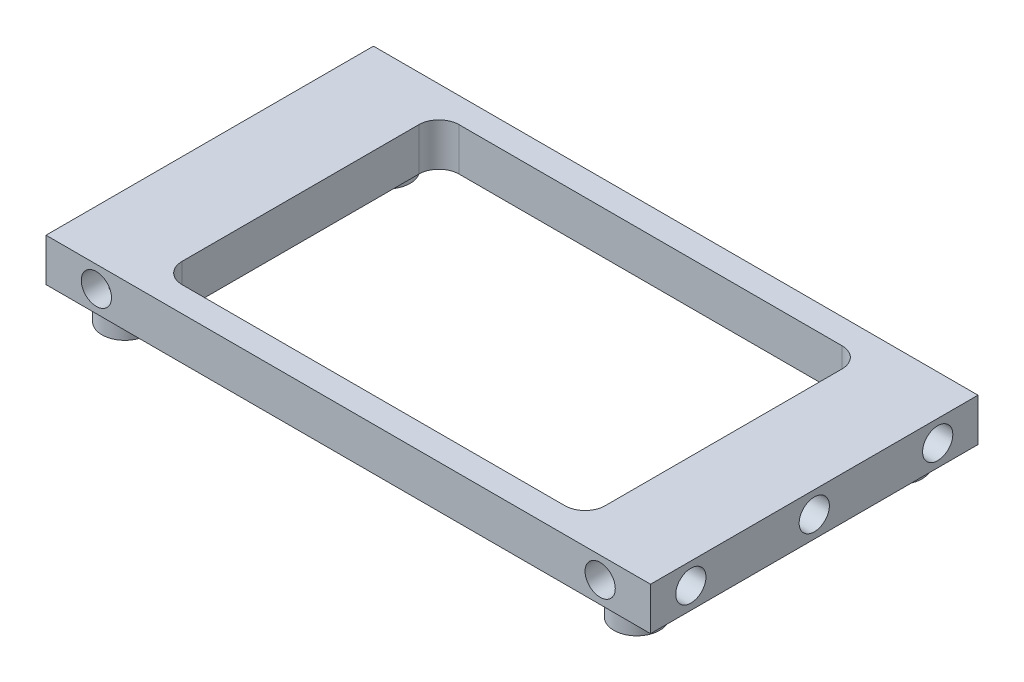
SolidWorks part; units mm, degrees
ref_plane "Front Plane" through (0, 0, 0) normal (0, 0, 1) x (1, 0, 0)
ref_plane "Top Plane" through (0, 0, 0) normal (0, 1, 0) x (1, 0, 0)
ref_plane "Right Plane" through (0, 0, 0) normal (1, 0, 0) x (0, 0, -1)
sketch "Sketch1" plane through (0, 0, 0) normal (1, 0, 0) x (0, 0, -1)
  line L1 (-32.5, -4.25) -> (32.5, -4.25)
  line L2 (-32.5, -4.25) -> (-32.5, 4.25)
  line L3 (-32.5, 4.25) -> (32.5, 4.25)
  line L4 (32.5, -4.25) -> (32.5, 4.25)
  line L5 (-32.5, -4.25) -> (32.5, 4.25) construction
  line L6 (-32.5, 4.25) -> (32.5, -4.25) construction
  point P0 (0, 0)
  dimension "D1" = 8.5
  dimension "D2" = 65
extrude "Boss-Extrude1" add sketch "Sketch1" along normal blind 120
hole_wizard "Ø6.0mm Dowel Hole1" positions "Sketch2" profile "Sketch3" hole size "Ø6.0" standard "ANSI Metric"
sketch "Sketch2" plane through (120, 0, 0) normal (1, 0, 0) x (0, 0, -1)
  line L0 (-32.5, 4.25) -> (-32.5, -4.25) construction
  line L1 (32.5, -4.25) -> (32.5, 4.25) construction
  point P0 (-24.5, 0)
  point P2 (0, 0)
  point P5 (24.5, 0)
  dimension "D1" = 8
  dimension "D2" = 8
sketch "Sketch3" plane through (120, 0, 24.5) normal (0, 1, 0) x (0, 0, -1)
  line L0 (0, 0) -> (0, 11.8026)
  line L1 (0, 11.8026) -> (3, 10)
  line L2 (3, 10) -> (3, 0)
  line L5 (3, 0) -> (0, 0)
  line L10 (0, 11.8026) -> (-3, 10) construction
  line L11 (0, -6.35) -> (0, 107.95) construction
  dimension "Hole Dia." = 6
  dimension "Hole Depth" = 10
  dimension "Drill Angle" = 118
ref_plane "Plane1" through (60, 0, 0) normal (1, 0, 0) x (0, 0, -1)
mirror "Mirror1" about plane through (60, 0, 0) normal (1, 0, 0) of "Ø6.0mm Dowel Hole1"
hole_wizard "Ø6.0mm Dowel Hole2" positions "Sketch4" profile "Sketch5" hole size "Ø6.0" standard "ANSI Metric"
sketch "Sketch4" plane through (0, 0, -32.5) normal (0, 0, -1) x (-1, 0, 0)
  line L0 (-120, -4.25) -> (-120, 4.25) construction
  line L1 (0, -4.25) -> (0, 4.25) construction
  line L2 (-120, 0) -> (0, 0) construction
  point P0 (-110, 0)
  point P2 (-10, 0)
  dimension "D1" = 10
  dimension "D2" = 10
sketch "Sketch5" plane through (110, 0, -32.5) normal (1, 0, 0) x (0, 1, 0)
  line L0 (0, 0) -> (0, 9.8026)
  line L1 (0, 9.8026) -> (3, 8)
  line L2 (3, 8) -> (3, 0)
  line L5 (3, 0) -> (0, 0)
  line L10 (0, 9.8026) -> (-3, 8) construction
  line L11 (0, -6.35) -> (0, 107.95) construction
  dimension "Hole Dia." = 6
  dimension "Hole Depth" = 8
  dimension "Drill Angle" = 118
mirror "Mirror2" about plane through (0, 0, 0) normal (0, 0, 1) of "Ø6.0mm Dowel Hole2"
sketch "Sketch6" plane through (0, 4.25, 0) normal (0, 1, 0) x (1, 0, 0)
  line L0 (86, -7) -> (86, 7) construction
  line L1 (80, -7) -> (80, 7)
  line L2 (92, -7) -> (92, 7)
  line L3 (120, 32.5) -> (120, -32.5) construction
  arc A0 (80, -7) -> (92, -7) centre (86, -7) ccw
  arc A1 (92, 7) -> (80, 7) centre (86, 7) ccw
  point P2 (86, 0)
  point P10 (120, 0)
  dimension "D3" = 12
  dimension "D1" = 40
  dimension "D2" = 14
extrude "Cut-Extrude1" cut sketch "Sketch6" against normal through all
mirror "Mirror3" about plane through (60, 0, 0) normal (1, 0, 0) of "Cut-Extrude1"
sketch "Sketch7" plane through (0, 4.25, 0) normal (0, 1, 0) x (1, 0, 0)
  line L0 (120, 32.5) -> (0, 32.5) construction
  line L1 (87, 17) -> (33, 17)
  line L2 (87, 17) -> (87, -17)
  line L3 (87, -17) -> (33, -17)
  line L4 (33, 17) -> (33, -17)
  line L5 (87, 17) -> (33, -17) construction
  line L6 (87, -17) -> (33, 17) construction
  point P0 (60, 0)
  point P8 (60, 32.5)
  dimension "D1" = 54
  dimension "D2" = 34
hole_wizard "Ø3.0mm Dowel Hole1" positions "Sketch8" profile "Sketch9" hole size "Ø3.0" standard "ANSI Metric" end condition through all
sketch "Sketch8" plane through (0, 4.25, 0) normal (0, 1, 0) x (1, 0, 0)
  line L0 (120, -32.5) -> (0, -32.5) construction
  line L1 (120, 32.5) -> (0, 32.5) construction
  line L2 (120, 32.5) -> (120, -32.5) construction
  line L3 (0, 32.5) -> (0, -32.5) construction
  point P0 (87, -17)
  point P3 (87, 17)
  point P6 (33, 17)
  point P9 (33, -17)
  point P13 (100, -24.5)
  point P15 (60, -24.5)
  point P17 (20, -24.5)
  point P19 (100, 24.5)
  point P21 (60, 24.5)
  point P23 (20, 24.5)
  point P40 (60, 32.5)
  dimension "D1" = 8
  dimension "D2" = 8
  dimension "D3" = 20
  dimension "D4" = 20
sketch "Sketch9" plane through (87, 4.25, 17) normal (1, 0, 0) x (0, 0, 1)
  line L0 (0, 0) -> (0, 8.5)
  line L1 (0, 8.5) -> (1.75, 8.5)
  line L2 (1.75, 8.5) -> (1.75, 0)
  line L5 (1.75, 0) -> (0, 0)
  line L11 (0, -6.35) -> (0, 107.95) construction
  dimension "Thru Hole Dia." = 3.5
  dimension "Thru Hole Depth" = 8.5
sketch "Sketch10" plane through (0, -4.25, 0) normal (0, -1, 0) x (1, 0, 0)
  line L0 (120, 32.5) -> (0, 32.5) construction
  line L1 (40, -21.5) -> (80, -21.5)
  line L2 (40, -21.5) -> (40, 21.5)
  line L3 (40, 21.5) -> (80, 21.5)
  line L4 (80, -21.5) -> (80, 21.5)
  line L5 (40, -21.5) -> (80, 21.5) construction
  line L6 (40, 21.5) -> (80, -21.5) construction
  line L7 (0, 32.5) -> (0, -32.5) construction
  line L8 (40, 21.5) -> (34, 13)
  line L9 (34, -13) -> (40, -21.5)
  line L10 (40, -7) -> (40, 7) construction
  line L11 (80, 21.5) -> (86, 13)
  line L12 (86, -13) -> (80, -21.5)
  arc A0 (40, 7) -> (28, 7) centre (34, 7) ccw construction
  arc A1 (28, -7) -> (40, -7) centre (34, -7) ccw construction
  arc A2 (28, -7) -> (40, -7) centre (34, -7) ccw
  arc A3 (40, 7) -> (28, 7) centre (34, 7) ccw
  arc A4 (80, -7) -> (92, -7) centre (86, -7) ccw construction
  arc A5 (92, 7) -> (80, 7) centre (86, 7) ccw construction
  arc A6 (80, -7) -> (92, -7) centre (86, -7) ccw
  arc A7 (92, 7) -> (80, 7) centre (86, 7) ccw
  point P0 (60, 0)
  point P7 (60, 32.5)
  point P11 (0, 0)
  line M17 (80, -7) -> (80, 7)
  arc M18 (80, 7) -> (92, 7) centre (86, 7) cw
  arc M20 (92, -7) -> (80, -7) centre (86, -7) cw
  arc M21 (28, 7) -> (40, 7) centre (34, 7) cw
  line M22 (40, 7) -> (40, -7)
  arc M23 (40, -7) -> (28, -7) centre (34, -7) cw
  dimension "D1" = 43
extrude "Cut-Extrude2" cut sketch "Sketch10" against normal through all contours L2 L8 M21 | L1 L4 L3 L2 M17 M22 | L9 L2 M23 | L11 L4 M18 | L12 L4 M20
fillet "Fillet1" radius 6 8 edges at (34, 0, -13) (40, 0, -21.5) (34, 0, 13) (40, 0, 21.5) (80, 0, -21.5) (86, 0, -13) (80, 0, 21.5) (86, 0, 13)
sketch "Sketch11" plane through (0, -4.25, 0) normal (0, -1, 0) x (1, 0, 0)
  line L0 (120, 32.5) -> (0, 32.5) construction
  line L1 (110.8, -26.035) -> (9.2, -26.035)
  line L2 (110.8, -26.035) -> (110.8, 26.035)
  line L3 (110.8, 26.035) -> (9.2, 26.035)
  line L4 (9.2, -26.035) -> (9.2, 26.035)
  line L5 (110.8, -26.035) -> (9.2, 26.035) construction
  line L6 (110.8, 26.035) -> (9.2, -26.035) construction
  line L7 (120, 32.5) -> (120, -32.5) construction
  circle A0 centre (9.2, 26.035) radius 2.55
  circle A1 centre (110.8, 26.035) radius 2.55
  circle A2 centre (110.8, -26.035) radius 2.55
  circle A3 centre (9.2, -26.035) radius 2.55
  circle A4 centre (9.2, 26.035) radius 4.55
  circle A5 centre (110.8, 26.035) radius 4.55
  circle A6 centre (110.8, -26.035) radius 4.55
  circle A7 centre (9.2, -26.035) radius 4.55
  point P0 (60, 0)
  point P11 (60, 32.5)
  point P14 (120, 0)
  dimension "D1" = 5.1
  dimension "D4" = 2
  dimension "D2" = 101.6
  dimension "D3" = 52.07
extrude "Boss-Extrude2" add sketch "Sketch11" along normal blind 5 contours L4 A7 L1 A3 | L1 A7 L4 A3 | L3 A4 L4 A0 | L4 A4 L3 A0 | L2 A5 L3 A1 | L3 A5 L2 A1 | L2 A6 L1 A2 | L1 A6 L2 A2
sketch "Sketch12" plane through (0, -4.25, 0) normal (0, -1, 0) x (1, 0, 0)
  circle A0 centre (110.8, -26.035) radius 2.55 construction
  circle A1 centre (110.8, 26.035) radius 2.55 construction
  circle A2 centre (9.2, 26.035) radius 2.55 construction
  circle A3 centre (9.2, -26.035) radius 2.55 construction
  circle A4 centre (110.8, -26.035) radius 2.55
  circle A5 centre (110.8, 26.035) radius 2.55
  circle A6 centre (9.2, 26.035) radius 2.55
  circle A7 centre (9.2, -26.035) radius 2.55
extrude "Cut-Extrude3" cut sketch "Sketch12" against normal blind 1.7
chamfer "Chamfer1" distance 1.5 angle 45 4 edges at (9.2, -4.25, -21.485) (110.8, -4.25, -21.485) (110.8, -4.25, 30.585) (9.2, -4.25, 30.585)
sketch "Sketch13" plane through (0, -4.25, 0) normal (0, -1, 0) x (1, 0, 0)
  line L0 (120, 32.5) -> (0, 32.5) construction
  line L1 (102, -27.5) -> (18, -27.5)
  line L2 (102, -27.5) -> (102, 27.5)
  line L3 (102, 27.5) -> (18, 27.5)
  line L4 (18, -27.5) -> (18, 27.5)
  line L5 (102, -27.5) -> (18, 27.5) construction
  line L6 (102, 27.5) -> (18, -27.5) construction
  line L7 (120, 32.5) -> (120, -32.5) construction
  point P0 (60, 0)
  point P7 (60, 32.5)
  point P10 (120, 0)
  dimension "D1" = 84
  dimension "D2" = 55
extrude "Cut-Extrude4" cut sketch "Sketch13" against normal through all
fillet "Fillet2" radius 4 4 edges at (102, 0, -27.5) (18, 0, -27.5) (18, 0, 27.5) (102, 0, 27.5)
